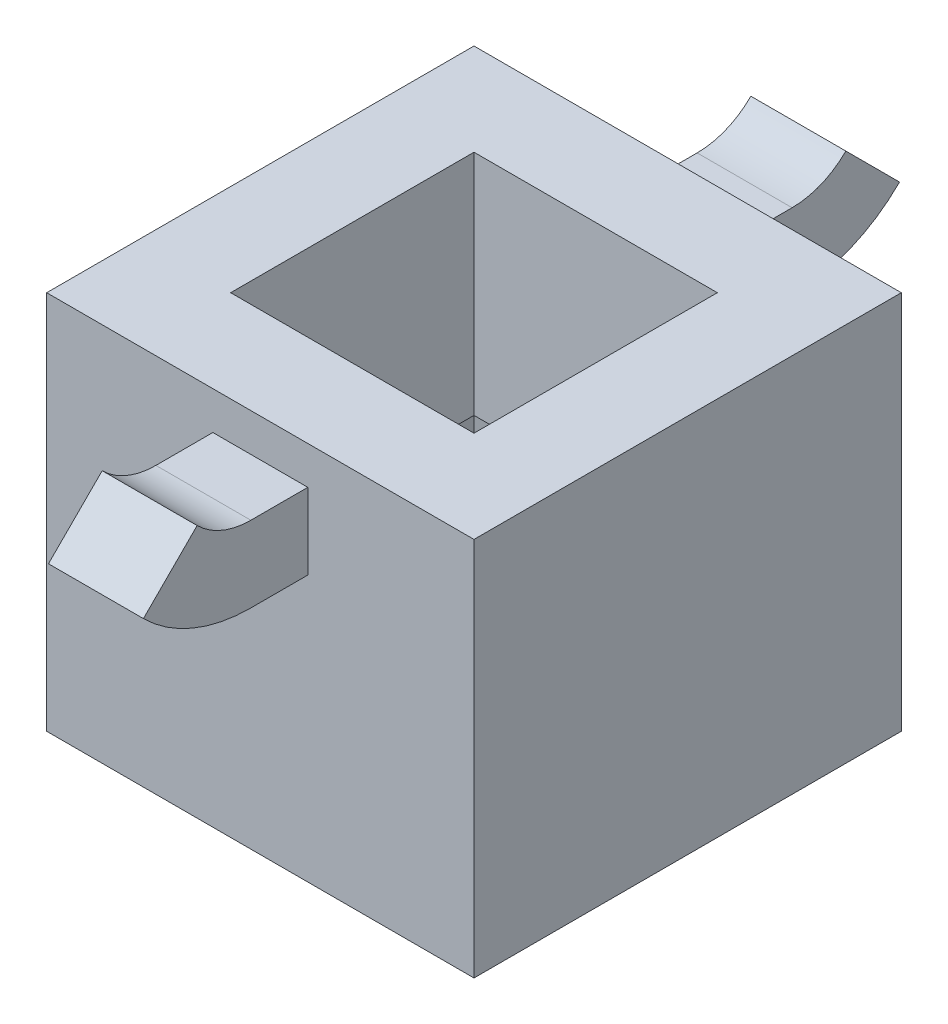
SolidWorks part; units mm, degrees
ref_plane "Front Plane" through (0, 0, 0) normal (0, 0, 1) x (1, 0, 0)
ref_plane "Top Plane" through (0, 0, 0) normal (0, 1, 0) x (1, 0, 0)
ref_plane "Right Plane" through (0, 0, 0) normal (1, 0, 0) x (0, 0, -1)
sketch "Sketch1" plane through (0, 0, 0) normal (0, 1, 0) x (1, 0, 0)
  line L1 (11.25, -11.25) -> (-11.25, -11.25)
  line L2 (11.25, -11.25) -> (11.25, 11.25)
  line L3 (11.25, 11.25) -> (-11.25, 11.25)
  line L4 (-11.25, -11.25) -> (-11.25, 11.25)
  line L5 (11.25, -11.25) -> (-11.25, 11.25) construction
  line L6 (11.25, 11.25) -> (-11.25, -11.25) construction
  point P0 (0, 0)
  dimension "D1" = 22.5
extrude "Boss-Extrude1" add sketch "Sketch1" along normal blind 20
sketch "Sketch3" plane through (0, 0, 0) normal (0, -1, 0) x (1, 0, 0)
  line L1 (-9.25, -9.25) -> (9.25, -9.25)
  line L2 (-9.25, -9.25) -> (-9.25, 9.25)
  line L3 (-9.25, 9.25) -> (9.25, 9.25)
  line L4 (9.25, -9.25) -> (9.25, 9.25)
  line L5 (-9.25, -9.25) -> (9.25, 9.25) construction
  line L6 (-9.25, 9.25) -> (9.25, -9.25) construction
  point P0 (0, 0)
  dimension "D1" = 18.5
sketch "Sketch5" plane through (0, 0, -11.25) normal (0, 0, -1) x (-1, 0, 0)
  line L0 (-11.25, 0) -> (11.25, 20) construction
  line L1 (-11.25, 20) -> (11.25, 0) construction
  line L2 (0, 16) -> (0, 10) construction
  line L3 (2.5, 18) -> (-2.5, 18)
  line L4 (2.5, 18) -> (2.5, 14)
  line L5 (2.5, 14) -> (-2.5, 14)
  line L6 (-2.5, 18) -> (-2.5, 14)
  line L7 (2.5, 18) -> (-2.5, 14) construction
  line L8 (2.5, 14) -> (-2.5, 18) construction
  dimension "D1" = 5
  dimension "D2" = 4
  dimension "D3" = 6
sketch "Sketch6" plane through (0, 0, 0) normal (1, 0, 0) x (0, 0, -1)
  line L0 (11.25, 16) -> (14.25, 16)
  arc A0 (14.25, 16) -> (18.4926, 17.7574) centre (14.25, 22) ccw
  dimension "D2" = 6
  dimension "D1" = 3
sweep "Sweep1" add profiles "Sketch5" path "Sketch6"
mirror "Mirror1" about plane through (0, 0, 0) normal (0, 0, 1) of "Sweep1"
extrude "Cut-Extrude5" cut sketch "Sketch3" against normal blind 6 draft 8
sketch "Sketch14" plane through (0, 6, 0) normal (0, -1, 0) x (1, 0, 0)
  line L1 (8.4068, 8.4068) -> (-8.4068, 8.4068)
  line L2 (8.4068, 8.4068) -> (8.4068, -8.4068)
  line L3 (8.4068, -8.4068) -> (-8.4068, -8.4068)
  line L4 (-8.4068, 8.4068) -> (-8.4068, -8.4068)
  line L5 (8.4068, 8.4068) -> (-8.4068, -8.4068) construction
  line L6 (8.4068, -8.4068) -> (-8.4068, 8.4068) construction
  point P0 (0, 0)
extrude "Cut-Extrude6" cut sketch "Sketch14" against normal blind 2
sketch "Sketch15" plane through (0, 8, 0) normal (0, -1, 0) x (1, 0, 0)
  line L0 (8.4068, 8.4068) -> (-8.4068, 8.4068) construction
  line L1 (6.4068, -6.4068) -> (-6.4068, -6.4068)
  line L2 (6.4068, -6.4068) -> (6.4068, 6.4068)
  line L3 (6.4068, 6.4068) -> (-6.4068, 6.4068)
  line L4 (-6.4068, -6.4068) -> (-6.4068, 6.4068)
  line L5 (6.4068, -6.4068) -> (-6.4068, 6.4068) construction
  line L6 (6.4068, 6.4068) -> (-6.4068, -6.4068) construction
  point P0 (0, 0)
  dimension "D1" = 2
extrude "Cut-Extrude7" cut sketch "Sketch15" against normal up to next
